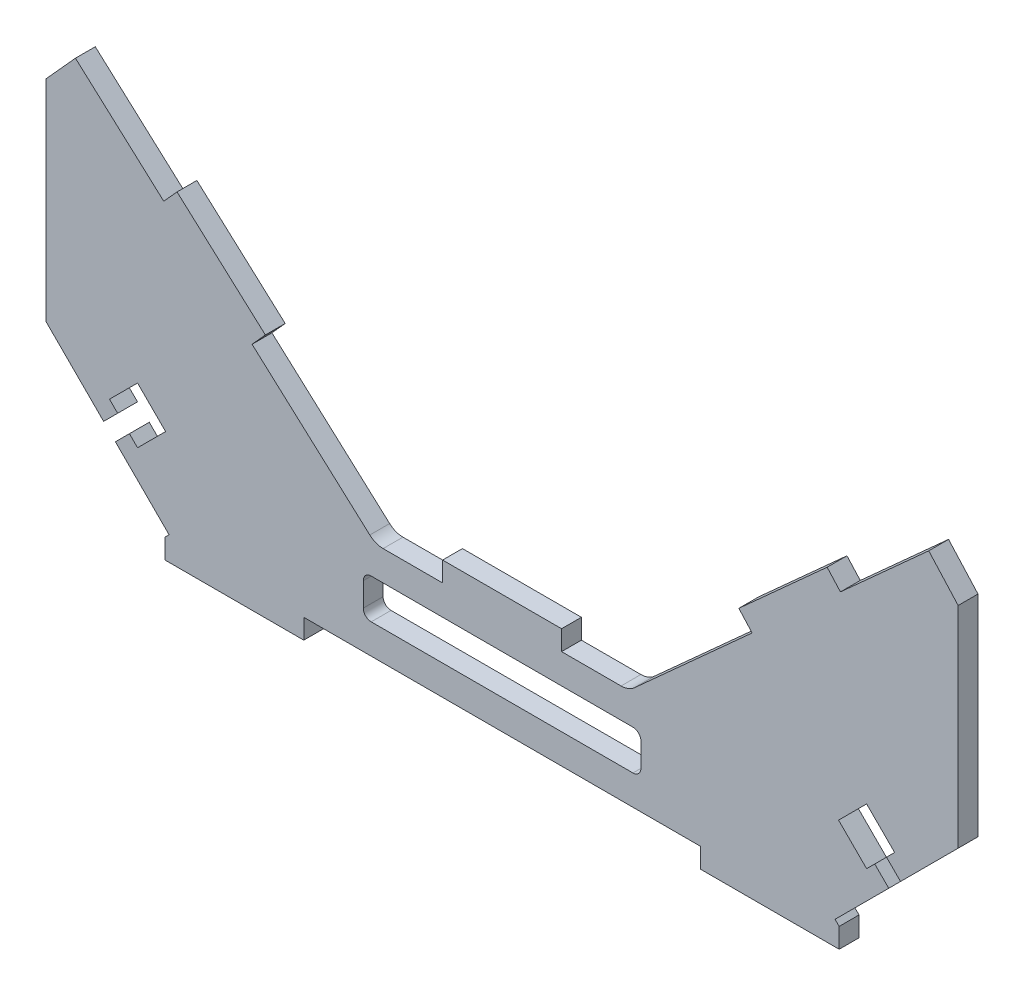
SolidWorks part; units mm, degrees
ref_plane "Front Plane" through (0, 0, 0) normal (0, 0, 1) x (1, 0, 0)
ref_plane "Top Plane" through (0, 0, 0) normal (0, 1, 0) x (1, 0, 0)
ref_plane "Right Plane" through (0, 0, 0) normal (1, 0, 0) x (0, 0, -1)
sketch "Sketch1" plane through (0, 0, 0) normal (0, 0, 1) x (1, 0, 0)
  line L0 (85, 25) -> (145, 25)
  line L1 (85, 25) -> (85, 30)
  line L2 (145, 25) -> (145, 30)
  line L3 (85, 30) -> (145, 30)
  line L4 (85, 30) -> (3.3505, 103.7113)
  line L5 (85, 30) -> (81.6495, 26.2887)
  line L6 (3.3505, 103.7113) -> (0, 100)
  line L7 (81.6495, 26.2887) -> (0, 100)
  line L8 (0, 100) -> (0, 0)
  line L9 (0, 0) -> (230, 0)
  line L10 (7.4227, 93.299) -> (0, 85.0769)
  line L11 (115, 0) -> (115, 30) construction
  line L12 (0, 35) -> (0, 65)
  line L16 (226.6495, 103.7113) -> (230, 100)
  line L17 (148.3505, 26.2887) -> (230, 100)
  line L18 (145, 30) -> (148.3505, 26.2887)
  line L19 (145, 30) -> (226.6495, 103.7113)
  line L23 (230, 35) -> (230, 65)
  line L24 (230, 100) -> (230, 0)
  line L25 (30, 0) -> (65, 0)
  line L26 (30, 0) -> (30, -5)
  line L27 (65, 0) -> (65, -5)
  line L28 (30, -5) -> (65, -5)
  line L30 (165, 0) -> (165, -5)
  line L31 (200, -5) -> (165, -5)
  line L32 (200, 0) -> (200, -5)
  line L33 (200, 0) -> (165, 0)
  line L35 (100, 25) -> (130, 25)
  line L36 (100, 25) -> (100, 30)
  line L37 (130, 25) -> (130, 30)
  line L38 (100, 30) -> (130, 30)
  line L39 (178.0412, 53.0928) -> (200.3093, 73.1959)
  line L40 (178.0412, 53.0928) -> (174.6907, 56.8041)
  line L41 (200.3093, 73.1959) -> (196.9588, 76.9072)
  line L42 (174.6907, 56.8041) -> (196.9588, 76.9072)
  line L43 (29.6907, 73.1959) -> (33.0412, 76.9072)
  line L44 (55.3093, 56.8041) -> (33.0412, 76.9072)
  line L45 (51.9588, 53.0928) -> (55.3093, 56.8041)
  line L46 (51.9588, 53.0928) -> (29.6907, 73.1959)
  line L47 (222.5773, 93.299) -> (230, 85.0769)
  arc A0 (81.6495, 26.2887) -> (85, 25) centre (85, 30) ccw
  arc A1 (148.3505, 26.2887) -> (145, 25) centre (145, 30) cw
  point P11 (115, 25)
  dimension "D1" = 60
  dimension "D2" = 5
  dimension "D3" = 5
  dimension "D4" = 110
  dimension "D5" = 100
  dimension "D6" = 25
  dimension "D7" = 10
  dimension "D11" = 5
  dimension "D12" = 35
  dimension "D13" = 30
  dimension "D14" = 30
  dimension "D15" = 5
  dimension "D16" = 15
  dimension "D17" = 5
  dimension "D18" = 40
  dimension "D19" = 30
extrude "Boss-Extrude1" add sketch "Sketch1" along normal blind 5
sketch "Sketch2" plane through (0, 0, 0) normal (0, 0, -1) x (-1, 0, 0)
  line L1 (-115, 0) -> (-115, 12.546) construction
  line L4 (0, 25) -> (0, 0)
  line L5 (0, 25) -> (-25, 0)
  line L6 (0, 0) -> (-25, 0)
  line L14 (-65, 0) -> (-165, 0) construction
  line L15 (-230, 0) -> (-205, 0)
  line L16 (-230, 25) -> (-205, 0)
  line L17 (-230, 25) -> (-230, 0)
  dimension "D1" = 25
  dimension "D2" = 25
extrude "Cut-Extrude1" cut sketch "Sketch2" against normal blind 10
sketch "Sketch3" plane through (0, 0, 0) normal (0, 0, -1) x (-1, 0, 0)
  line L0 (-115, 0) -> (-115, 6.1037) construction
  line L1 (-82, 7.5) -> (-93.5, 7.5)
  line L2 (-80, 9.5) -> (-80, 15.5)
  line L3 (-82, 17.5) -> (-93.5, 17.5)
  line L4 (-95.5, 9.5) -> (-95.5, 15.5)
  line L5 (-65, 0) -> (-165, 0) construction
  line L10 (-65, 0) -> (-65, -5) construction
  line L11 (-134.5, 9.5) -> (-134.5, 15.5)
  line L12 (-148, 17.5) -> (-136.5, 17.5)
  line L13 (-150, 9.5) -> (-150, 15.5)
  line L14 (-148, 7.5) -> (-136.5, 7.5)
  arc A4 (-93.5, 7.5) -> (-95.5, 9.5) centre (-93.5, 9.5) cw
  arc A5 (-93.5, 17.5) -> (-95.5, 15.5) centre (-93.5, 15.5) ccw
  arc A6 (-80, 15.5) -> (-82, 17.5) centre (-82, 15.5) ccw
  arc A7 (-82, 7.5) -> (-80, 9.5) centre (-82, 9.5) ccw
  arc A8 (-148, 7.5) -> (-150, 9.5) centre (-148, 9.5) cw
  arc A9 (-150, 15.5) -> (-148, 17.5) centre (-148, 15.5) cw
  arc A10 (-136.5, 17.5) -> (-134.5, 15.5) centre (-136.5, 15.5) cw
  arc A11 (-136.5, 7.5) -> (-134.5, 9.5) centre (-136.5, 9.5) ccw
  point P22 (-150, 7.5)
  point P23 (-150, 17.5)
  point P24 (-134.5, 17.5)
  point P25 (-134.5, 7.5)
  point P28 (-95.5, 7.5)
  point P31 (-95.5, 17.5)
  point P34 (-80, 17.5)
  point P37 (-80, 7.5)
  dimension "D1" = 15.5
  dimension "D2" = 10
  dimension "D3" = 7.5
  dimension "D4" = 15
extrude "Cut-Extrude2" cut sketch "Sketch3" against normal blind 10
sketch "Sketch5" plane through (12.5, 12.5, 0) normal (-0.7071, -0.7071, 0) x (0, 0, 1)
  line L1 (5, -21.2132) -> (0, -21.2132) construction
  line L3 (0, -21.2132) -> (0, 22.7757)
  line L4 (0, 22.7757) -> (5, 22.7757)
  line L5 (5, -21.2132) -> (5, 22.7757)
  line L6 (5, -21.2132) -> (0, -21.2132)
  dimension "D1" = 5
extrude "Cut-Extrude4" cut sketch "Sketch5" against normal blind 5
ref_plane "Plane1" through (115, 0, 0) normal (1, 0, 0) x (0, 0, -1)
mirror "Mirror1" about plane through (115, 0, 0) normal (1, 0, 0) of "Cut-Extrude4"
sketch "Sketch6" plane through (0, 0, 0) normal (0, 0, -1) x (-1, 0, 0)
  line L0 (-178.0412, 53.0928) -> (-178.0412, 59.8289)
  line L1 (-174.6907, 56.8041) -> (-196.9588, 76.9072) construction
  line L2 (-178.0412, 59.8289) -> (-174.6907, 56.8041)
  line L3 (-174.6907, 56.8041) -> (-178.0412, 53.0928)
  line L4 (-115, 30) -> (-115, 17.1246) construction
  line L5 (-100, 30) -> (-130, 30) construction
  line L6 (-55.3093, 56.8041) -> (-51.9588, 53.0928)
  line L7 (-51.9588, 59.8289) -> (-55.3093, 56.8041)
  line L8 (-51.9588, 53.0928) -> (-51.9588, 59.8289)
extrude "Cut-Extrude5" [suppressed] cut sketch "Sketch6" against normal blind 5
sketch "Sketch7" plane through (0, 0, 0) normal (0, 0, -1) x (-1, 0, 0)
  line L0 (-16.0151, 16.056) -> (-28.7056, 28.7466) construction
  line L1 (0, 32.0711) -> (-31.0355, 1.0355) construction
  line L2 (-17.5, 14.5711) -> (-14.5302, 17.5409)
  line L3 (-17.5, 14.5711) -> (-21.0355, 18.1066)
  line L4 (-14.5302, 17.5409) -> (-18.0657, 21.0765)
  line L5 (-21.0355, 18.1066) -> (-18.0657, 21.0765)
  line L6 (-16.0151, 23.1271) -> (-23.0861, 16.056)
  line L7 (-16.0151, 23.1271) -> (-23.0861, 30.1981)
  line L8 (-23.0861, 16.056) -> (-30.1572, 23.1271)
  line L9 (-23.0861, 30.1981) -> (-30.1572, 23.1271)
  line L10 (-30, 0) -> (-30, -5) construction
  line L11 (-115, 0) -> (-115, 9.9331) construction
  line L12 (-65, 0) -> (-165, 0) construction
  line L13 (-213.9849, 16.056) -> (-201.2944, 28.7466) construction
  line L14 (-206.9139, 30.1981) -> (-199.8428, 23.1271)
  line L15 (-206.9139, 16.056) -> (-199.8428, 23.1271)
  line L16 (-213.9849, 23.1271) -> (-206.9139, 30.1981)
  line L17 (-213.9849, 23.1271) -> (-206.9139, 16.056)
  line L18 (-208.9645, 18.1066) -> (-211.9343, 21.0765)
  line L19 (-215.4698, 17.5409) -> (-211.9343, 21.0765)
  line L20 (-212.5, 14.5711) -> (-208.9645, 18.1066)
  line L21 (-212.5, 14.5711) -> (-215.4698, 17.5409)
  point P4 (-26.6217, 26.6626)
  point P11 (-16.0151, 16.056)
  line M30 (-230, 32.0711) -> (-198.9645, 1.0355)
  line M40 (-31.0355, 1.0355) -> (0, 32.0711)
  dimension "D1" = 4.2
  dimension "D2" = 10
  dimension "D3" = 5
  dimension "D4" = 10
  dimension "D5" = 12.5
extrude "Cut-Extrude6" cut sketch "Sketch7" against normal blind 10 contours L7 L9 L8 L6 L5 | L5 L3 L4 M40 | L16 L17 L15 L14 | L20 L17 L19 M30
sketch "Sketch8" plane through (0, 0, 0) normal (0, 0, -1) x (-1, 0, 0)
  line L0 (-136.5, 17.5) -> (-93.5, 17.5)
  line L1 (-93.5, 17.5) -> (-93.5, 7.5)
  line L2 (-93.5, 7.5) -> (-136.5, 7.5)
  line L3 (-136.5, 7.5) -> (-136.5, 17.5)
extrude "Cut-Extrude7" cut sketch "Sketch8" against normal blind 10
